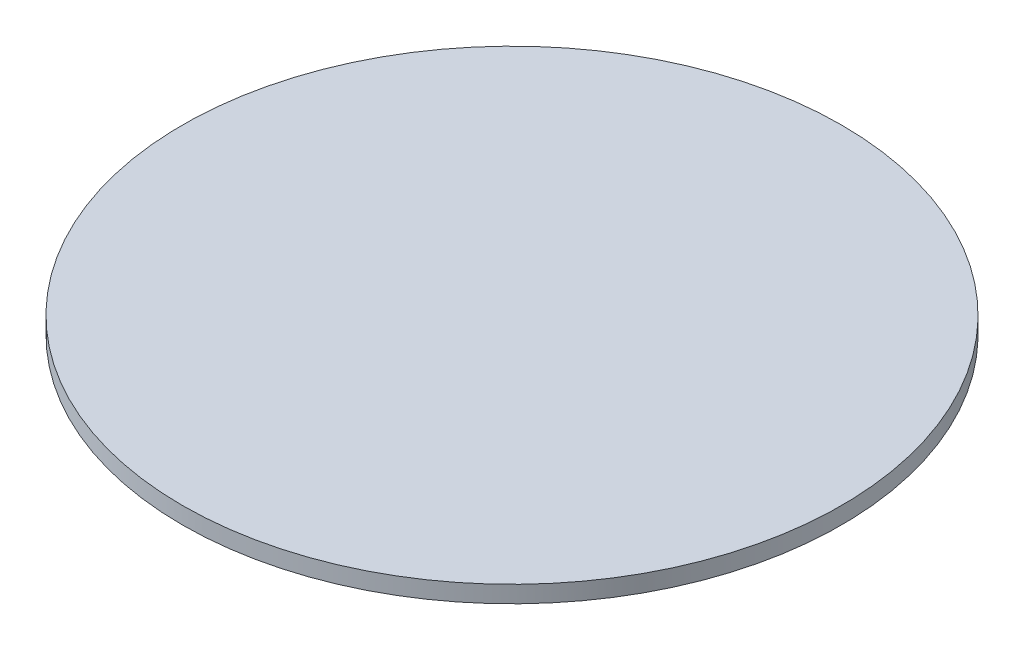
SolidWorks part; units mm, degrees
ref_plane "Front Plane" through (0, 0, 0) normal (0, 0, 1) x (1, 0, 0)
ref_plane "Top Plane" through (0, 0, 0) normal (0, 1, 0) x (1, 0, 0)
ref_plane "Right Plane" through (0, 0, 0) normal (1, 0, 0) x (0, 0, -1)
sketch "Sketch1" plane through (0, 0, 0) normal (0, 1, 0) x (1, 0, 0)
  circle A0 centre (0, 0) radius 19.5
extrude "Boss-Extrude1" add sketch "Sketch1" along normal blind 1
